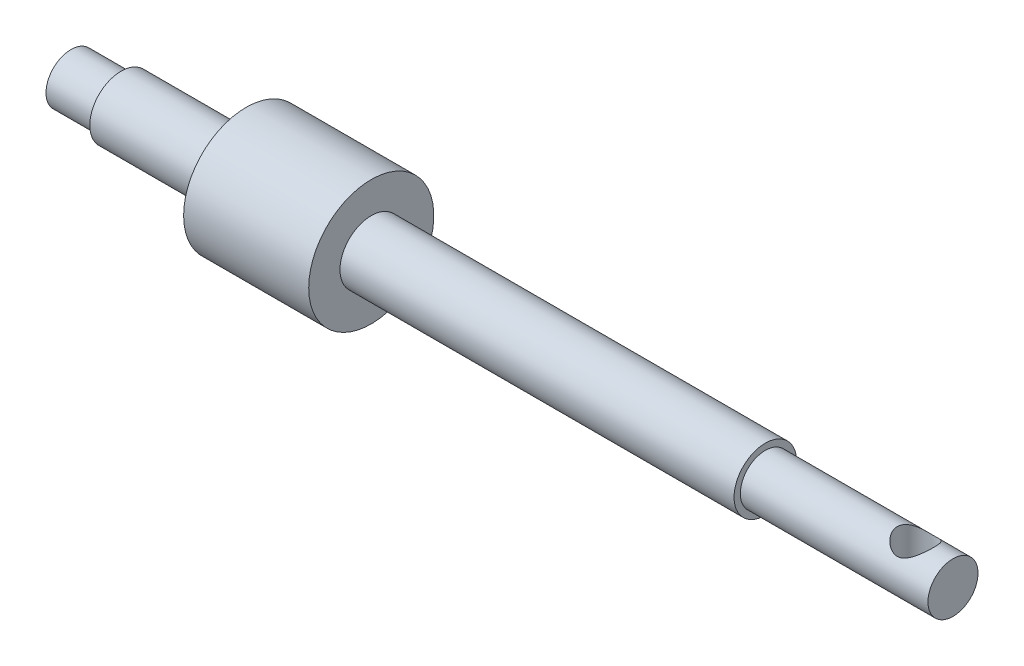
SolidWorks part; units mm, degrees
material "普通碳钢"
ref_plane "前视基准面" through (0, 0, 0) normal (0, 0, 1) x (1, 0, 0)
ref_plane "上视基准面" through (0, 0, 0) normal (0, 1, 0) x (1, 0, 0)
ref_plane "右视基准面" through (0, 0, 0) normal (1, 0, 0) x (0, 0, -1)
sketch "草图1" plane through (0, 0, 0) normal (0, 0, 1) x (1, 0, 0)
  line L0 (-56.4792, 0) -> (68.0925, 0) construction
  line L1 (-52.4792, 2.5) -> (-52.4792, 2)
  line L2 (-52.4792, 2.5) -> (-42.4792, 2.5)
  line L3 (-42.4792, 2.5) -> (-42.4792, 5)
  line L4 (-42.4792, 5) -> (-32.4792, 5)
  line L5 (-32.4792, 5) -> (-32.4792, 2.5)
  line L6 (-32.4792, 2.5) -> (-0.9792, 2.5)
  line L7 (-0.9792, 2.5) -> (-0.9792, 2)
  line L8 (-0.9792, 2) -> (12.0208, 2)
  line L9 (12.0208, 2) -> (12.0208, 0)
  line L10 (-52.4792, 2) -> (-56.4792, 2)
  line L11 (-56.4792, 2) -> (-56.4792, 0)
  line L12 (-56.4792, 0) -> (12.0208, 0)
  dimension "D1" = 10
  dimension "D2" = 13
  dimension "D3" = 4
  dimension "D4" = 10
  dimension "D5" = 31.5
  dimension "D6" = 4
  dimension "D7" = 5
  dimension "D8" = 10
  dimension "D9" = 2.5
  dimension "D10" = 2
revolve "旋转1" add sketch "草图1" angle 360 about L0
sketch "草图2" plane through (12.0208, 0, 0) normal (1, 0, 0) x (0, 0, -1)
  circle A1 centre (0, 0) radius 2
extrude "凸台-拉伸1" add sketch "草图2" along normal blind 2
sketch "草图4" plane through (14.0208, 0, 0) normal (1, 0, 0) x (0, 0, -1)
  line L0 (0, 0) -> (-1.9997, 0.0368)
  circle A0 centre (0, 0) radius 2 construction
sketch "草图5" plane through (0, 0, 0) normal (0, 1, 0) x (1, 0, 0)
  line L0 (14.0208, 0) -> (11.0208, 0) construction
  circle A0 centre (11.0208, 0) radius 1.45
  dimension "D1" = 3
extrude "切除-拉伸4" cut sketch "草图5" against normal mid plane 10
